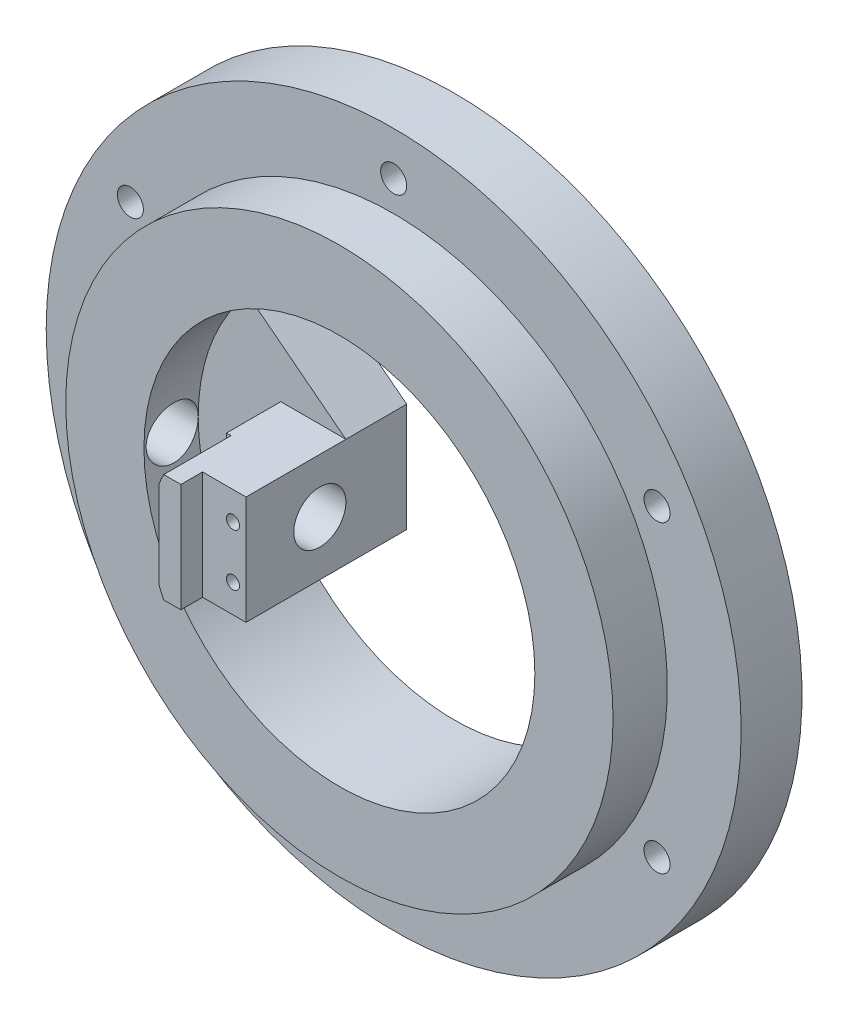
SolidWorks part; units mm, degrees
ref_plane "Front Plane" through (0, 0, 0) normal (0, 0, 1) x (1, 0, 0)
ref_plane "Top Plane" through (0, 0, 0) normal (0, 1, 0) x (1, 0, 0)
ref_plane "Right Plane" through (0, 0, 0) normal (1, 0, 0) x (0, 0, -1)
sketch "Sketch1" plane through (0, 0, 0) normal (0, 0, 1) x (1, 0, 0)
  circle A0 centre (0, 0) radius 45
  circle A1 centre (0, 0) radius 70
  dimension "D1" = 90
  dimension "D2" = 140
extrude "Boss-Extrude1" add sketch "Sketch1" along normal blind 4
sketch "Sketch3" plane through (0, 0, 0) normal (0, 0, 1) x (1, 0, 0)
  circle A0 centre (0, 0) radius 60
  circle A1 centre (0, 0) radius 45
extrude "Boss-Extrude4" add sketch "Sketch3" along normal blind 32
sketch "Sketch6" plane through (0, 0, 0) normal (0, 1, 0) x (1, 0, 0)
  line L0 (-70, -4) -> (70, -4) construction
  line L1 (-11, -4) -> (29, -4) construction
  line L2 (-11, -4) -> (-11, -32) construction
  line L3 (-11, -32) -> (29, -32) construction
  line L4 (29, -4) -> (29, -32) construction
  line L5 (-60, -32) -> (60, -32) construction
  line L6 (-45, 0) -> (-45, -32) construction
  line L7 (45, -32) -> (29, -32)
  line L8 (45, -32) -> (45, -22)
  line L9 (45, -22) -> (29, -22)
  line L10 (29, -32) -> (29, -22)
  line L11 (-11, -32) -> (-45, -32)
  line L12 (-11, -32) -> (-11, -22)
  line L13 (-11, -22) -> (-45, -22)
  line L14 (-45, -32) -> (-45, -22)
  dimension "D1" = 40
  dimension "D2" = 11
  dimension "D3" = 10
  dimension "D4" = 10
extrude "Boss-Extrude5" add sketch "Sketch6" along normal mid plane 25
ref_plane "Plane1" through (9, 0, 0) normal (1, 0, 0) x (0, 0, -1)
sketch "Sketch10" plane through (0, 0, 0) normal (0, 1, 0) x (1, 0, 0)
  line L0 (45, 0) -> (-45, 0) construction
  line L1 (-11, -22) -> (-26, -22)
  line L2 (-11, -22) -> (-11, 0)
  line L3 (-11, 0) -> (-26, 0)
  line L4 (-26, -22) -> (-26, 0)
  dimension "D1" = 15
extrude "Boss-Extrude6" add sketch "Sketch10" along normal mid plane 25
sketch "Sketch11" plane through (0, 0, 0) normal (0, 1, 0) x (1, 0, 0)
  line L0 (-70, -4) -> (70, -4) construction
  line L1 (-11, -4) -> (-45, -4)
  line L2 (-11, -4) -> (-11, 0)
  line L3 (-11, 0) -> (-45, 0)
  line L4 (-45, -4) -> (-45, 0)
  line L5 (-11, -32) -> (-11, 0) construction
extrude "Boss-Extrude7" add sketch "Sketch11" along normal mid plane 60
sketch "Sketch12" plane through (0, 0, 0) normal (0, 1, 0) x (1, 0, 0)
  line L0 (-43.229, -32) -> (43.229, -32) construction
  line L1 (-43.229, -22) -> (-26, -22)
  line L2 (-43.229, -22) -> (-43.229, -32)
  line L3 (-43.229, -32) -> (-26, -32)
  line L4 (-26, -22) -> (-26, -32)
extrude "Cut-Extrude3" cut sketch "Sketch12" against normal mid plane 25
sketch "Sketch13" plane through (0, 0, 0) normal (0, 0, 1) x (1, 0, 0)
  line L0 (-33.541, 30) -> (-11, 12.5)
  line L1 (-33.541, 30) -> (-11, 30) construction
  line L2 (-11, 12.5) -> (-11, 30)
  line L3 (-11, 30) -> (-33.541, 30)
  arc A0 (43.229, 12.5) -> (-43.229, 12.5) centre (0, 0) ccw construction
extrude "Cut-Extrude4" cut sketch "Sketch13" against normal mid plane 25
sketch "Sketch14" plane through (0, 0, 0) normal (0, 0, 1) x (1, 0, 0)
  line L0 (-33.541, -30) -> (-11, -12.5)
  line L1 (-11, -12.5) -> (-11, -30)
  line L2 (-11, -30) -> (-33.541, -30)
extrude "Cut-Extrude5" cut sketch "Sketch14" against normal mid plane 25
sketch "Sketch17" plane through (0, 0, 32) normal (0, 0, 1) x (1, 0, 0)
  line L0 (43.229, 12.5) -> (27.2718, 12.5)
  line L1 (43.229, -12.5) -> (27.2718, -12.5)
  arc A0 (27.2718, 12.5) -> (27.2718, -12.5) centre (0, 0) ccw
  circle A1 centre (0, 0) radius 45
  dimension "D1" = 60
sketch "Sketch20" plane through (0, 0, 32) normal (0, 0, 1) x (1, 0, 0)
  line L0 (-11, 12.5) -> (-21, 12.5)
  line L1 (-11, 12.5) -> (-26, 12.5) construction
  line L2 (-21, 12.5) -> (-21, -12.5)
  line L3 (-11, -12.5) -> (-26, -12.5) construction
  line L4 (-21, -12.5) -> (-11, -12.5)
  line L5 (-11, -12.5) -> (-11, 12.5)
  line L6 (9, -5.5) -> (9, 5.5) construction
  line L7 (29, -12.5) -> (29, 12.5)
  line L8 (39, -12.5) -> (29, -12.5)
  line L9 (39, 12.5) -> (39, -12.5)
  line L10 (29, 12.5) -> (39, 12.5)
  dimension "D1" = 10
extrude "Cut-Extrude11" cut sketch "Sketch20" against normal blind 4
sketch "Sketch21" plane through (0, 0, 32) normal (0, 0, 1) x (1, 0, 0)
  circle A0 centre (0, 0) radius 32.5
  circle A1 centre (0, 0) radius 45
extrude "Boss-Extrude8" add sketch "Sketch21" against normal blind 15
sketch "Sketch22" plane through (0, 0, 32) normal (0, 0, 1) x (1, 0, 0)
  line L1 (26.0658, -12.5) -> (43.229, -12.5)
  line L2 (26.0658, -12.5) -> (26.0658, 12.5)
  line L3 (26.0658, 12.5) -> (43.229, 12.5)
  line L4 (43.229, -12.5) -> (43.229, 12.5)
  line L5 (26.0658, -12.5) -> (43.229, 12.5) construction
  line L6 (26.0658, 12.5) -> (43.229, -12.5) construction
  point P0 (34.6474, 0)
extrude "Cut-Extrude12" cut sketch "Sketch22" against normal blind 5
sketch "Sketch25" plane through (0, 0, 4) normal (0, 0, 1) x (1, 0, 0)
  circle A0 centre (0, 0) radius 60
  circle A1 centre (0, 0) radius 63
extrude "Boss-Extrude9" add sketch "Sketch25" along normal blind 50
sketch "Sketch26" plane through (0, 0, 0) normal (0, 0, -1) x (-1, 0, 0)
  circle A0 centre (0, 0) radius 70
  circle A1 centre (0, 0) radius 80
  dimension "D1" = 160
extrude "Boss-Extrude10" add sketch "Sketch26" against normal up to surface (4 mm away) up to face at (70, 0, 4)
sketch "Sketch29" plane through (0, 0, 4) normal (0, 0, 1) x (1, 0, 0)
  circle A0 centre (0, 0) radius 70
  circle A1 centre (0, 70) radius 3
  circle A2 centre (60.6218, 35) radius 3
  circle A3 centre (60.6218, -35) radius 3
  circle A4 centre (0, -70) radius 3
  circle A5 centre (-60.6218, -35) radius 3
  circle A6 centre (-60.6218, 35) radius 3
  point P18 (0, 0)
  dimension "D1" = 6
extrude "Cut-Extrude14" cut sketch "Sketch29" against normal blind 5 contours A0 A6 | A0 A6 | A0 A1 | A0 A2 | A0 A2 | A0 A3 | A0 A3 | A0 A4 | A0 A4 | A0 A5 | A0 A5 | A0 A1
sketch "Sketch30" plane through (0, 0, 0) normal (0, 0, -1) x (-1, 0, 0)
  line L0 (11, -12.5) -> (33.541, -30) construction
  line L1 (11, 12.5) -> (11, -12.5) construction
  line L2 (33.541, 30) -> (11, 12.5) construction
  line L3 (11, -12.5) -> (33.541, -30)
  line L4 (11, 12.5) -> (11, -12.5)
  line L5 (33.541, 30) -> (11, 12.5)
  arc A0 (33.541, 30) -> (33.541, -30) centre (0, 0) ccw construction
  circle A1 centre (-60.6218, 35) radius 3 construction
  circle A2 centre (-60.6218, -35) radius 3 construction
  circle A3 centre (0, -70) radius 3 construction
  circle A4 centre (60.6218, -35) radius 3 construction
  circle A5 centre (60.6218, 35) radius 3 construction
  circle A6 centre (0, 70) radius 3 construction
  circle A7 centre (0, 0) radius 80 construction
  arc A8 (33.541, 30) -> (33.541, -30) centre (0, 0) ccw
  circle A9 centre (-60.6218, 35) radius 3
  circle A10 centre (-60.6218, -35) radius 3
  circle A11 centre (0, -70) radius 3
  circle A12 centre (60.6218, -35) radius 3
  circle A13 centre (60.6218, 35) radius 3
  circle A14 centre (0, 70) radius 3
  circle A15 centre (0, 0) radius 80
extrude "Boss-Extrude11" add sketch "Sketch30" along normal blind 10
sketch "Sketch16" plane through (-11, 0, 0) normal (1, 0, 0) x (0, 0, -1)
  circle A0 centre (-10, 0) radius 6
  dimension "D1" = 12
  dimension "D2" = 10
extrude "Cut-Extrude10" cut sketch "Sketch16" against normal blind 100
sketch "Sketch31" plane through (0, 0, 28) normal (0, 0, 1) x (1, 0, 0)
  line L0 (-11, 12.5) -> (-26, 12.5) construction
  line L1 (21, -12.5) -> (-21, -12.5)
  line L2 (21, -12.5) -> (21, 12.5)
  line L3 (21, 12.5) -> (-21, 12.5)
  line L4 (-21, -12.5) -> (-21, 12.5)
  line L5 (21, -12.5) -> (-21, 12.5) construction
  line L6 (21, 12.5) -> (-21, -12.5) construction
  line L7 (-26, 12.5) -> (-21, 12.5) construction
  point P0 (0, 0)
extrude "Cut-Extrude15" cut sketch "Sketch31" against normal up to surface (1 mm away) up to face at (34.0763, 0, 27)
ref_plane "Plane2" through (0, 0, 17) normal (0, 0, -1) x (-1, 0, 0)
sketch "Sketch33" plane through (0, 0, 54) normal (0, 0, 1) x (1, 0, 0)
  circle A0 centre (0, 0) radius 27.8998
  circle A1 centre (0, 0) radius 81.7973
extrude "Cut-Extrude17" cut sketch "Sketch33" against normal blind 37.5
sketch "Sketch34" plane through (0, 0, 27) normal (0, 0, 1) x (1, 0, 0)
  line L0 (-11, 12.5) -> (-11, -12.5) construction
  circle A0 centre (-14, 6) radius 1.5
  circle A1 centre (-14, -6) radius 1.5
  dimension "D3" = 3
  dimension "D4" = 3
  dimension "D1" = 12
  dimension "D2" = 6
  dimension "D5" = 3
  dimension "D6" = 3
extrude "Cut-Extrude18" cut sketch "Sketch34" against normal blind 10
